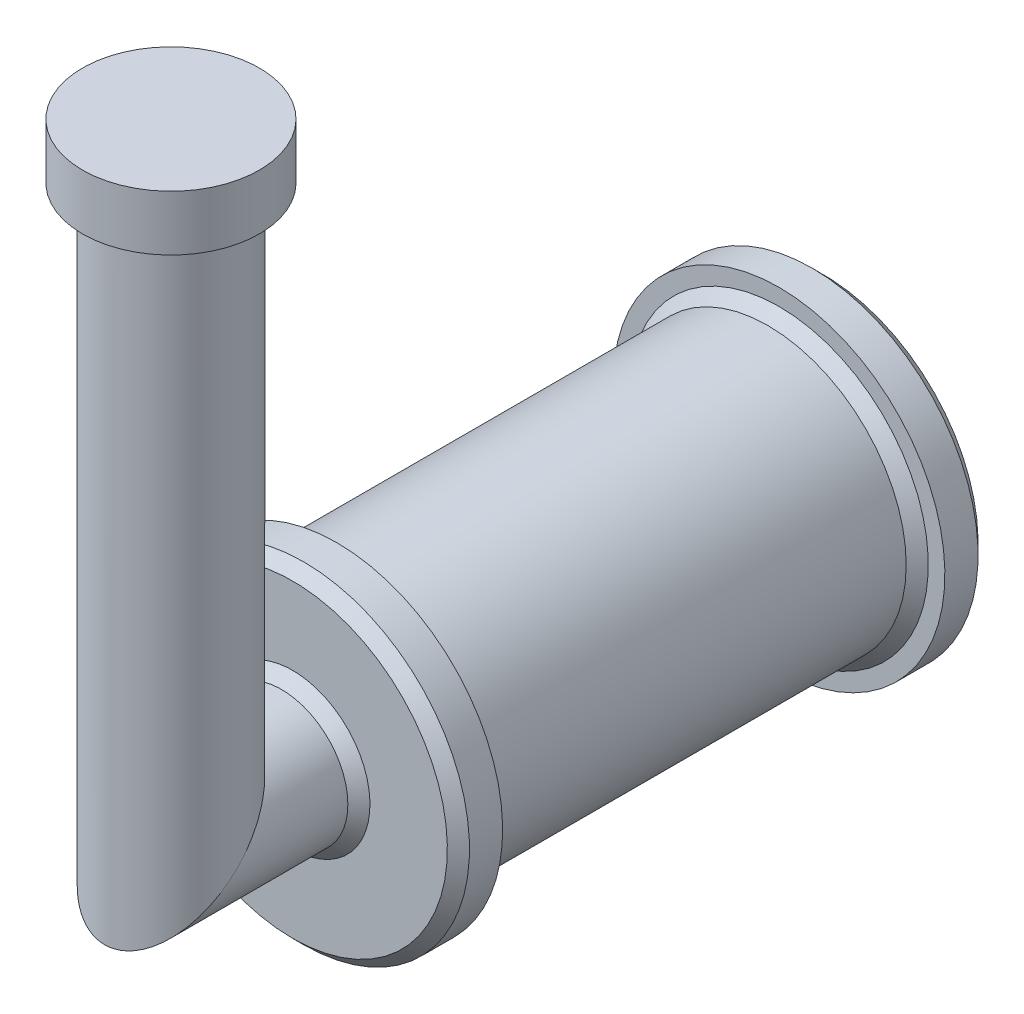
SolidWorks part; units mm, degrees
material "Balsa"
ref_plane "Front Plane" through (0, 0, 0) normal (0, 0, 1) x (1, 0, 0)
ref_plane "Top Plane" through (0, 0, 0) normal (0, 1, 0) x (1, 0, 0)
ref_plane "Right Plane" through (0, 0, 0) normal (1, 0, 0) x (0, 0, -1)
sketch "Sketch1" plane through (0, 0, 0) normal (1, 0, 0) x (0, 0, -1)
  line L0 (0, 695.9709) -> (0, 0)
  line L1 (0, 0) -> (737.5, 0)
  dimension "D1" = 695.9709
  dimension "D2" = 737.5
ref_plane "Plane1" through (0, 695.9709, 0) normal (0, 1, 0) x (1, 0, 0)
sketch "Sketch2" plane through (0, 695.9709, 0) normal (0, 1, 0) x (1, 0, 0)
  circle A0 centre (0, 0) radius 75
  dimension "D1" = 150
sweep "Sweep1" add profiles "Sketch2" path "Sketch1"
sketch "Sketch3" plane through (0, 695.9709, 0) normal (0, 1, 0) x (1, 0, 0)
  circle A0 centre (0, 0) radius 100
  dimension "D1" = 200
extrude "Boss-Extrude1" add sketch "Sketch3" against normal blind 62.5
sketch "Sketch4" plane through (0, 0, 0) normal (1, 0, 0) x (0, 0, -1)
  line L0 (737.5, 75) -> (75, 75) construction
  line L2 (137.5, 75) -> (137.5, 187.5)
  line L3 (137.5, 187.5) -> (187.5, 187.5)
  line L4 (187.5, 156.25) -> (187.5, 187.5)
  line L5 (737.5, 0) -> (634.2346, 0) construction
  line L6 (187.5, 156.25) -> (687.5, 156.25)
  line L10 (737.5, 75) -> (137.5, 75)
  line L11 (737.5, 75) -> (737.5, 187.5)
  line L12 (737.5, 187.5) -> (687.5, 187.5)
  line L13 (687.5, 156.25) -> (687.5, 187.5)
  line L14 (737.5, -75) -> (737.5, 75) construction
  line L15 (737.5, -75) -> (737.5, 75) construction
  dimension "D1" = 187.5
  dimension "D2" = 156.25
  dimension "D3" = 50
  dimension "D4" = 500
revolve "Revolve1" add sketch "Sketch4" angle 360 about L5
chamfer "Chamfer1" distance 12.5 angle 45 5 edges at (0, 75, -137.5) (0, 187.5, -137.5) (0, 187.5, -737.5) (0, 156.25, -687.5) (0, 156.25, -187.5)
